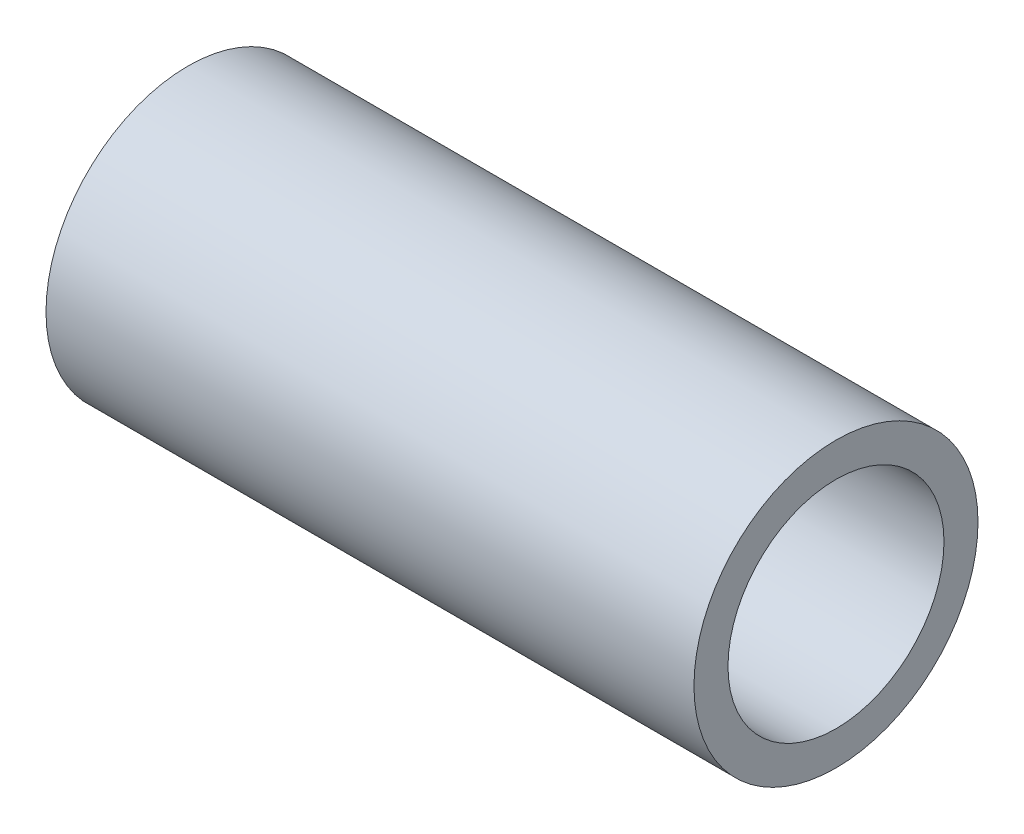
SolidWorks part; units mm, degrees
material "6061-T6 (SS)"
ref_plane "Front Plane" through (0, 0, 0) normal (0, 0, 1) x (1, 0, 0)
ref_plane "Top Plane" through (0, 0, 0) normal (0, 1, 0) x (1, 0, 0)
ref_plane "Right Plane" through (0, 0, 0) normal (1, 0, 0) x (0, 0, -1)
sketch "Sketch1" plane through (0, 0, 0) normal (1, 0, 0) x (0, 0, -1)
  circle A0 centre (0, 0) radius 16.7005
  circle A1 centre (0, 0) radius 12.7
  dimension "D1" = 33.401
  dimension "D2" = 25.4
extrude "Boss-Extrude1" add sketch "Sketch1" along normal blind 76.2
